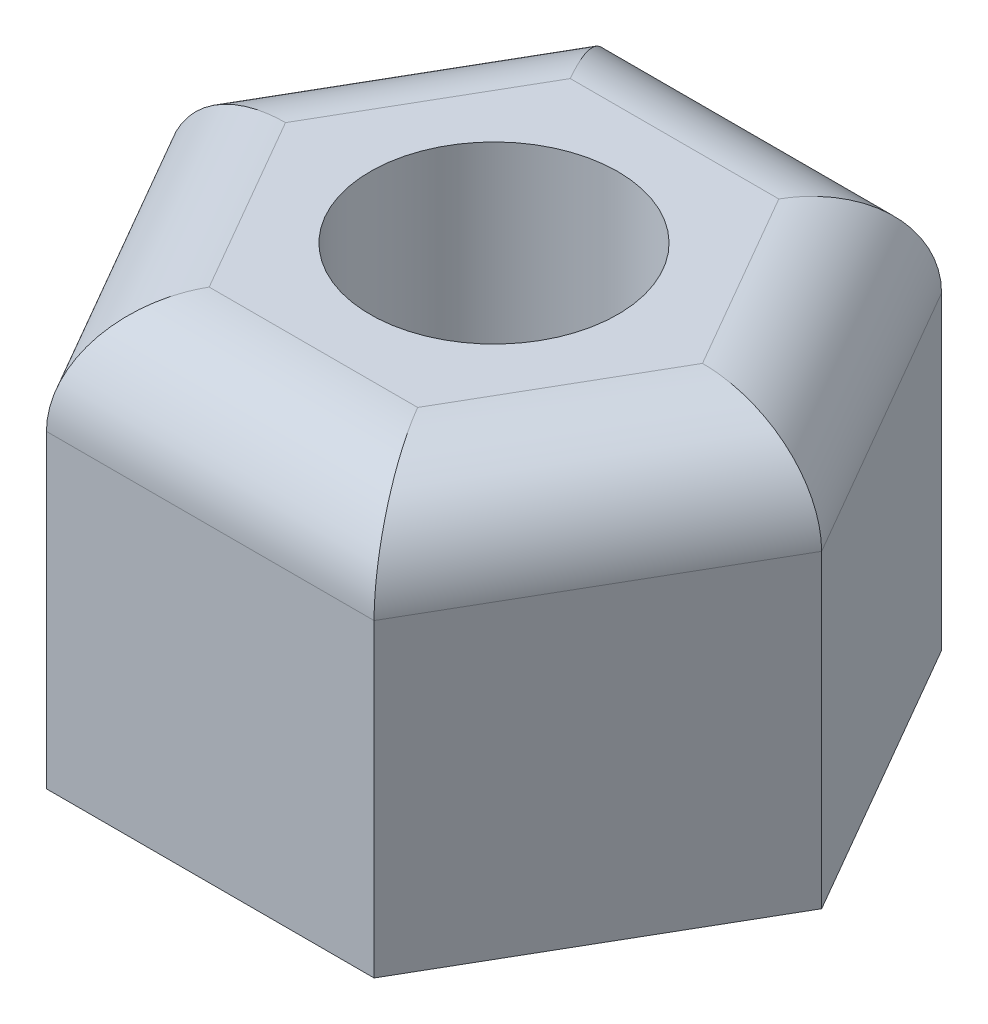
SolidWorks part; units mm, degrees
ref_plane "Front Plane" through (0, 0, 0) normal (0, 0, 1) x (1, 0, 0)
ref_plane "Top Plane" through (0, 0, 0) normal (0, 1, 0) x (1, 0, 0)
ref_plane "Right Plane" through (0, 0, 0) normal (1, 0, 0) x (0, 0, -1)
sketch "Sketch2" plane through (0, 0, 0) normal (0, 1, 0) x (1, 0, 0)
  line L1 (3.1754, 0) -> (1.5877, 2.75)
  line L2 (1.5877, 2.75) -> (-1.5877, 2.75)
  line L3 (-1.5877, 2.75) -> (-3.1754, 0)
  line L4 (-3.1754, 0) -> (-1.5877, -2.75)
  line L5 (-1.5877, -2.75) -> (1.5877, -2.75)
  line L6 (1.5877, -2.75) -> (3.1754, 0)
  circle A0 centre (0, 0) radius 2.75 construction
  dimension "D1" = 5.5
extrude "Boss-Extrude2" add sketch "Sketch2" along normal blind 4
fillet "Fillet1" radius 1 6 edges at (0, 4, 2.75) (-2.3816, 4, 1.375) (-2.3816, 4, -1.375) (0, 4, -2.75) (2.3816, 4, -1.375) (2.3816, 4, 1.375)
sketch "Sketch3" plane through (0, 0, 0) normal (0, -1, 0) x (1, 0, 0)
  circle A0 centre (0, 0) radius 1.2
extrude "Cut-Extrude1" cut sketch "Sketch3" against normal through all
